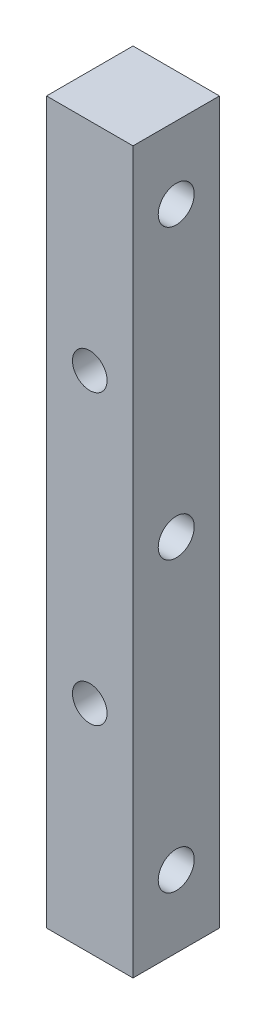
SolidWorks part; units mm, degrees
material "6061-T6 (SS)"
ref_plane "前视基准面" through (0, 0, 0) normal (0, 0, 1) x (1, 0, 0)
ref_plane "上视基准面" through (0, 0, 0) normal (0, 1, 0) x (1, 0, 0)
ref_plane "右视基准面" through (0, 0, 0) normal (1, 0, 0) x (0, 0, -1)
sketch "草图1" plane through (0, 0, 0) normal (0, 0, 1) x (1, 0, 0)
  line L1 (0, 0) -> (6, 0)
  line L2 (0, 0) -> (0, 70)
  line L3 (0, 70) -> (6, 70)
  line L4 (6, 0) -> (6, 70)
  dimension "D1" = 6
  dimension "D2" = 70
extrude "凸台-拉伸1" add sketch "草图1" along normal blind 6
sketch "草图4" plane through (0, 0, 0) normal (-1, 0, 0) x (0, 0, 1)
  line L0 (3, 70) -> (3, 65) construction
  line L1 (6, 70) -> (0, 70) construction
  line L2 (3, 65) -> (3, 45) construction
  line L3 (3, 45) -> (3, 25) construction
  line L4 (3, 25) -> (3, 5) construction
  line L5 (3, 5) -> (3, 0) construction
  line L6 (6, 0) -> (0, 0) construction
  circle A0 centre (3, 65) radius 1.25
  circle A1 centre (3, 45) radius 1.25
  circle A2 centre (3, 25) radius 1.25
  circle A3 centre (3, 5) radius 1.25
  dimension "D2" = 2.5
  dimension "D1" = 20
extrude "切除-拉伸3" cut sketch "草图4" against normal blind 8
cosmetic thread "装饰螺纹线13" parameters "D2"=3
cosmetic thread "装饰螺纹线14" parameters "D2"=3
cosmetic thread "装饰螺纹线15" parameters "D2"=3
cosmetic thread "装饰螺纹线16" parameters "D2"=3
sketch "草图6" plane through (0, 0, 6) normal (0, 0, 1) x (1, 0, 0)
  line L0 (3, 70) -> (3, 55) construction
  line L1 (6, 70) -> (0, 70) construction
  line L2 (3, 55) -> (3, 35) construction
  line L3 (3, 35) -> (3, 15) construction
  line L4 (3, 15) -> (3, 0) construction
  line L5 (0, 0) -> (6, 0) construction
  line L6 (6, 0) -> (6, 70) construction
  line L7 (3, 75) -> (3, 55) construction
  line L8 (3, 70) -> (3, 170) construction
  line L10 (0, 170) -> (6, 170) construction
  line L11 (0, 170) -> (0, -100) construction
  line L12 (0, -100) -> (6, -100) construction
  line L13 (6, 170) -> (6, -100) construction
  circle A4 centre (3, 15) radius 1.2
  circle A5 centre (3, 35) radius 1.2
  circle A6 centre (3, 55) radius 1.2
  dimension "D3" = 2.4
  dimension "D1" = 20
  dimension "D2" = 3
  dimension "D4" = 100
  dimension "D5" = 100
  dimension "D6" = 6
extrude "切除-拉伸5" cut sketch "草图6" against normal blind 10
cosmetic thread "装饰螺纹线17" parameters "D2"=3
cosmetic thread "装饰螺纹线18" parameters "D2"=3
cosmetic thread "装饰螺纹线19" parameters "D2"=3
sketch "草图7" plane through (0, 70, 0) normal (0, 1, 0) x (1, 0, 0)
  line L4 (6, 0) -> (0, 0)
  line L5 (0, 0) -> (0, -6)
  line L6 (0, -6) -> (6, -6)
  line L7 (6, -6) -> (6, 0)
  line L8 (6, 0) -> (0, 0)
  line L9 (0, 0) -> (0, -6)
  line L10 (0, -6) -> (6, -6)
  line L11 (6, -6) -> (6, 0)
  dimension "D1" = 0
extrude "切除-拉伸6" cut sketch "草图7" against normal blind 20
move or copy body "实体-移动/复制1" [suppressed] bodies to move or copy 120
